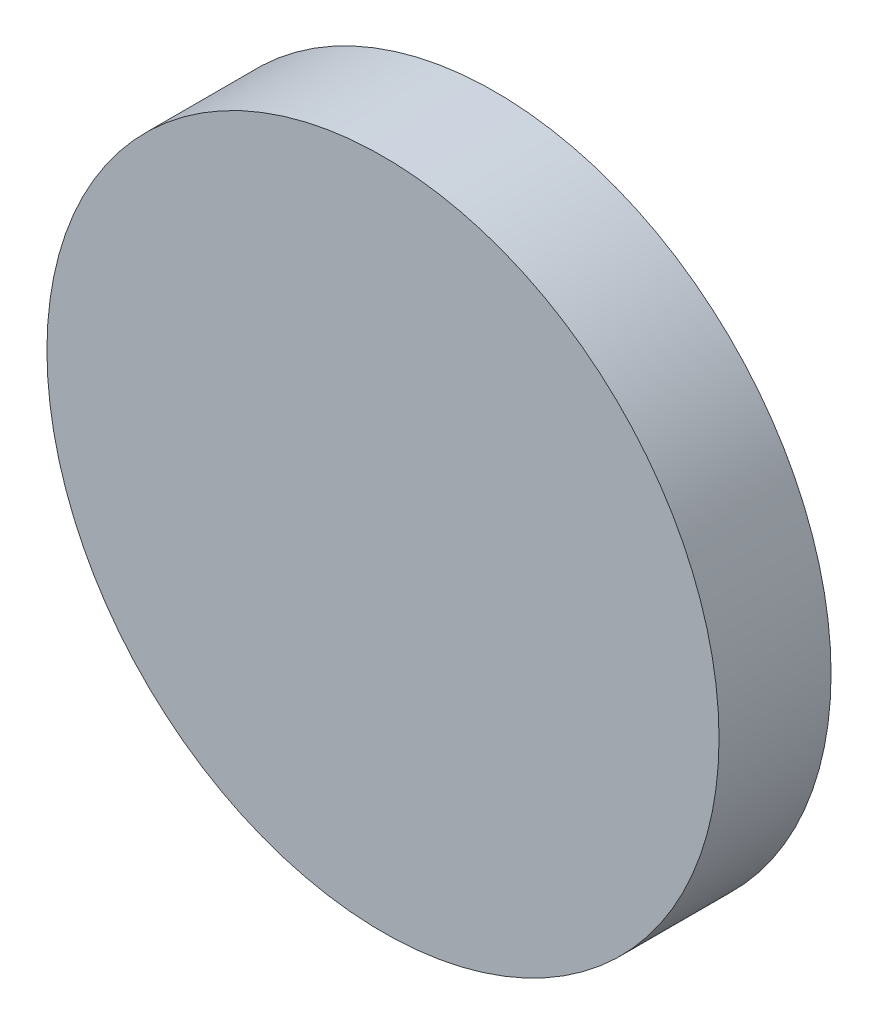
SolidWorks part; units mm, degrees
ref_plane "前视基准面" through (0, 0, 0) normal (0, 0, 1) x (1, 0, 0)
ref_plane "上视基准面" through (0, 0, 0) normal (0, 1, 0) x (1, 0, 0)
ref_plane "右视基准面" through (0, 0, 0) normal (1, 0, 0) x (0, 0, -1)
sketch "草图1" plane through (0, 0, 0) normal (0, 0, 1) x (1, 0, 0)
  circle A0 centre (0, 0) radius 1.5
  dimension "D1" = 3
extrude "凸台-拉伸1" add sketch "草图1" along normal blind 0.5 contours A0
